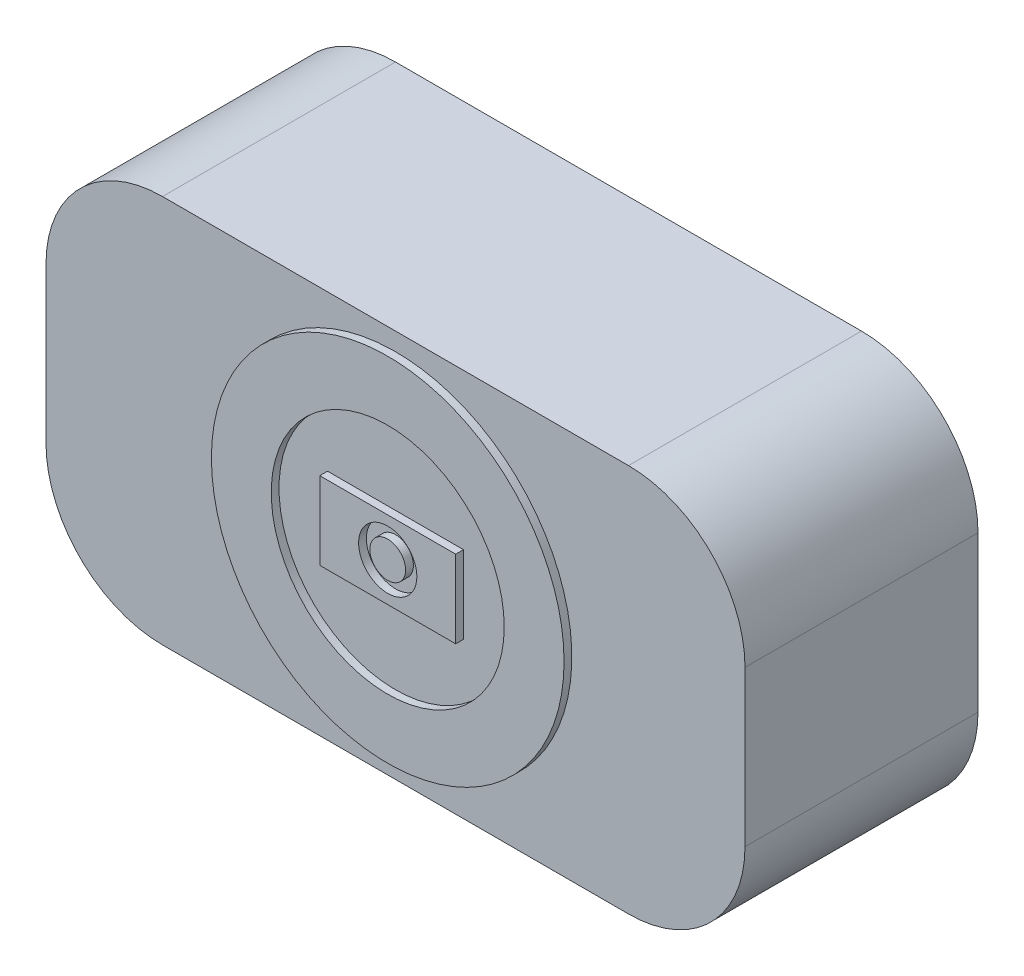
SolidWorks part; units mm, degrees
ref_plane "Front Plane" through (0, 0, 0) normal (0, 0, 1) x (1, 0, 0)
ref_plane "Top Plane" through (0, 0, 0) normal (0, 1, 0) x (1, 0, 0)
ref_plane "Right Plane" through (0, 0, 0) normal (1, 0, 0) x (0, 0, -1)
sketch "Sketch1" plane through (0, 0, 0) normal (0, 0, 1) x (1, 0, 0)
  line L1 (0, 0) -> (90, 0)
  line L2 (0, 0) -> (0, 50)
  line L3 (0, 50) -> (90, 50)
  line L4 (90, 0) -> (90, 50)
  dimension "D1" = 90
  dimension "D2" = 50
extrude "Boss-Extrude1" add sketch "Sketch1" against normal blind 30
fillet "Fillet1" radius 15 4 edges at (90, 0, -15) (0, 0, -15) (0, 50, -15) (90, 50, -15)
sketch "Sketch2" plane through (0, 0, 0) normal (0, 0, 1) x (1, 0, 0)
  circle A4 centre (45, 25) radius 22.7034
extrude "Boss-Extrude2" add sketch "Sketch2" along normal blind 1
sketch "Sketch3" plane through (0, 0, 1) normal (0, 0, 1) x (1, 0, 0)
  circle A0 centre (45, 25) radius 15
  dimension "D1" = 30
extrude "Cut-Extrude1" cut sketch "Sketch3" against normal blind 1
sketch "Sketch4" plane through (0, 0, 0) normal (0, 0, 1) x (1, 0, 0)
  line L0 (75, 50) -> (15, 50) construction
  line L1 (36.25, 20) -> (53.75, 20)
  line L2 (36.25, 20) -> (36.25, 30)
  line L3 (36.25, 30) -> (53.75, 30)
  line L4 (53.75, 20) -> (53.75, 30)
  line L5 (90, 15) -> (90, 35) construction
  point P4 (45, 30)
  dimension "D1" = 17.5
  dimension "D2" = 10
  dimension "D3" = 20
  dimension "D4" = 36.25
extrude "Boss-Extrude3" add sketch "Sketch4" along normal blind 1
sketch "Sketch5" plane through (0, 0, 1) normal (0, 0, 1) x (1, 0, 0)
  circle A0 centre (45, 25) radius 3.75
  dimension "D1" = 7.5
extrude "Cut-Extrude2" cut sketch "Sketch5" against normal blind 1
sketch "Sketch6" plane through (0, 0, 0) normal (0, 0, 1) x (1, 0, 0)
  circle A0 centre (45, 25) radius 2.3033
extrude "Boss-Extrude4" add sketch "Sketch6" along normal blind 1
